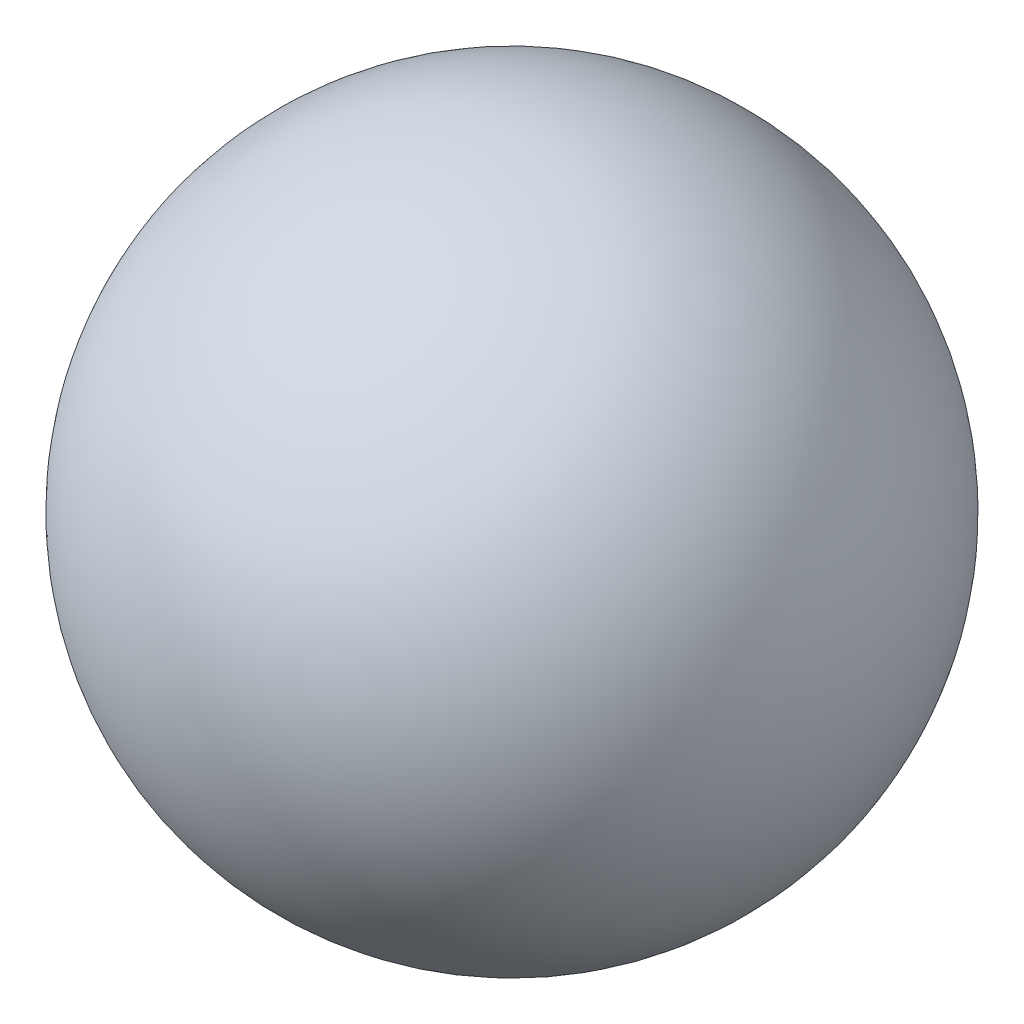
SolidWorks part; units mm, degrees
ref_plane "Front Plane" through (0, 0, 0) normal (0, 0, 1) x (1, 0, 0)
ref_plane "Top Plane" through (0, 0, 0) normal (0, 1, 0) x (1, 0, 0)
ref_plane "Right Plane" through (0, 0, 0) normal (1, 0, 0) x (0, 0, -1)
sketch "Sketch1" plane through (0, 0, 0) normal (0, 0, 1) x (1, 0, 0)
  line L0 (-14.3015, 0) -> (21.5166, 0) construction
  line L1 (-12, 0) -> (12, 0)
  arc A0 (12, 0) -> (-12, 0) centre (0, 0) ccw
  dimension "D1" = 24
revolve "Revolve1" add sketch "Sketch1" angle 360 about L0
